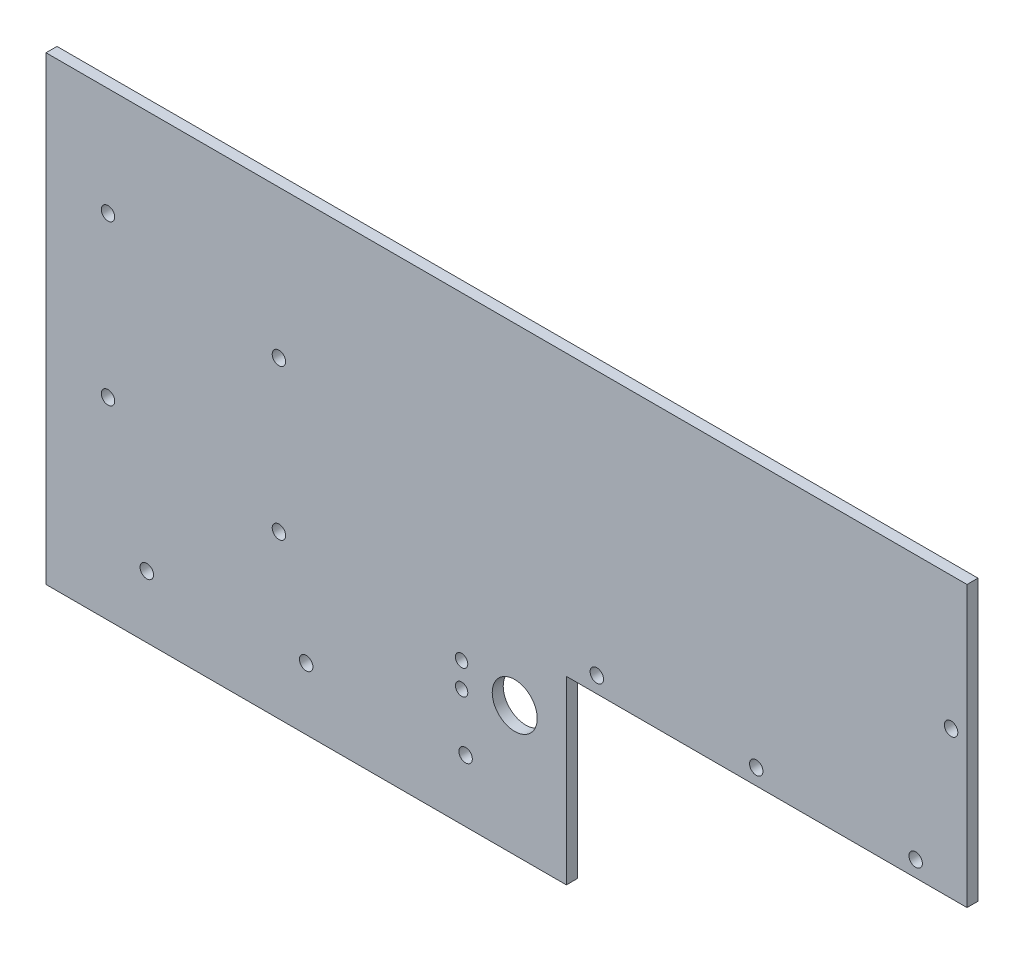
SolidWorks part; units mm, degrees
ref_plane "Front Plane" through (0, 0, 0) normal (0, 0, 1) x (1, 0, 0)
ref_plane "Top Plane" through (0, 0, 0) normal (0, 1, 0) x (1, 0, 0)
ref_plane "Right Plane" through (0, 0, 0) normal (1, 0, 0) x (0, 0, -1)
sketch "Sketch1" plane through (0, 0, 0) normal (0, 0, 1) x (1, 0, 0)
  line L0 (130, -14) -> (16.9, -14)
  line L1 (-130, -65) -> (16.9, -65)
  line L2 (-130, -65) -> (-130, 65)
  line L3 (-130, 65) -> (130, 65)
  line L4 (130, -14) -> (130, 65)
  line L5 (-130, -65) -> (130, 65) construction
  line L6 (-130, 65) -> (130, -65) construction
  line L7 (16.9, -14) -> (16.9, -65)
  point P0 (0, 0)
  dimension "D1" = 260
  dimension "D2" = 130
  dimension "D3" = 113.1
  dimension "D4" = 51
extrude "Boss-Extrude1" add sketch "Sketch1" along normal blind 3.1
sketch "Sketch2" plane through (0, 0, 0) normal (0, 0, -1) x (-1, 0, 0)
  point P0 (-115.5, -9.5)
  point P1 (-70.5, -9.5)
  point P3 (-25.5, -9.5)
  point P5 (-125.5, 27.5)
  point P7 (11.5498, -47.5)
  point P9 (56.5498, -47.5)
  point P11 (101.5498, -47.5)
  point P13 (64.2444, -19.2328)
  point P15 (64.2444, 23.2672)
  point P17 (112.4995, 34.5024)
  point P19 (112.4995, -10.4976)
hole_wizard "#6 Clearance Hole1" positions "Sketch3" profile "Sketch4" hole size "#6" standard "ANSI Inch" end condition through all
sketch "Sketch3" plane through (0, 0, 3.1) normal (0, 0, 1) x (1, 0, 0)
  point P0 (25.5, -9.5)
  point P3 (70.5, -9.5)
  point P6 (115.5, -9.5)
  point P10 (-11.5498, -47.5)
  point P13 (-56.5498, -47.5)
  point P16 (-101.5498, -47.5)
  point P19 (125.5, 27.5)
  point P23 (-64.2444, -19.2328)
  point P26 (-64.2444, 23.2672)
  point P39 (0, 0)
  point P40 (0, 0)
sketch "Sketch4" plane through (25.5, -9.5, 3.1) normal (1, 0, 0) x (0, -1, 0)
  line L0 (0, 0) -> (0, 3.1)
  line L1 (0, 3.1) -> (1.8986, 3.1)
  line L2 (1.8986, 3.1) -> (1.8986, 0)
  line L5 (1.8986, 0) -> (0, 0)
  line L11 (0, -6.35) -> (0, 107.95) construction
  dimension "Thru Hole Dia." = 3.7973
  dimension "Thru Hole Depth" = 3.1
hole_wizard "#6 Clearance Hole2" positions "Sketch5" profile "Sketch7" hole size "#6" standard "ANSI Inch" end condition through all
sketch "Sketch5" plane through (0, 0, 3.1) normal (0, 0, 1) x (1, 0, 0)
  point P0 (-112.4995, 34.5024)
  point P3 (-112.4995, -10.4976)
sketch "Sketch7" plane through (-112.4995, 34.5024, 3.1) normal (1, 0, 0) x (0, -1, 0)
  line L0 (0, 0) -> (0, 3.1)
  line L1 (0, 3.1) -> (1.8986, 3.1)
  line L2 (1.8986, 3.1) -> (1.8986, 0)
  line L5 (1.8986, 0) -> (0, 0)
  line L11 (0, -6.35) -> (0, 107.95) construction
  dimension "Thru Hole Dia." = 3.7973
  dimension "Thru Hole Depth" = 3.1
sketch "Sketch8" plane through (0, 0, 0) normal (0, 0, -1) x (-1, 0, 0)
  line L0 (-2.3174, -28.4196) -> (27.6826, -28.4196) construction
  line L1 (12.6826, -24.9196) -> (12.6826, -31.9196) construction
  circle A0 centre (-2.3174, -28.4196) radius 6.35
  circle A1 centre (12.6826, -24.9196) radius 1.75
  circle A2 centre (12.6826, -31.9196) radius 1.75
  point P6 (12.6826, -28.4196)
  point P8 (0, 0)
  dimension "D1" = 12.7
  dimension "D2" = 3.5
  dimension "D3" = 15
  dimension "D4" = 7
extrude "Cut-Extrude1" cut sketch "Sketch8" against normal through all
